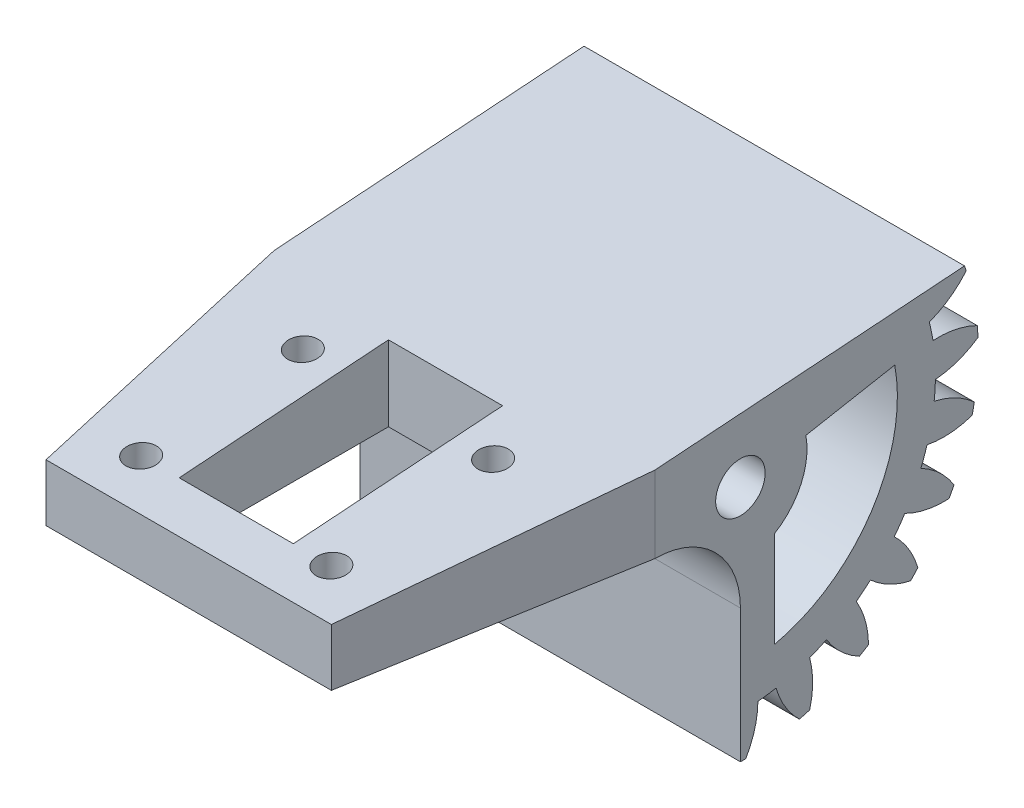
SolidWorks part; units mm, degrees
ref_plane "Plane1" through (0, 0, 0) normal (0, 0, 1) x (1, 0, 0)
ref_plane "Plane2" through (0, 0, 0) normal (0, 1, 0) x (1, 0, 0)
ref_plane "Plane3" through (0, 0, 0) normal (1, 0, 0) x (0, 0, -1)
other "Configuration Table"
sketch "HoldingSke" plane through (0, 0, 0) normal (0, 1, 0) x (1, 0, 0)
  line L0 (0, 0) -> (0.4603, -0.1954)
  line L1 (-15, 0) -> (100, 0) construction
  line L2 (0, 0) -> (-2.1039, 2.3779)
  line L3 (0, 0) -> (-11.863, 4.5341)
  line L4 (0, 0) -> (7.9495, 3.3744)
  line L5 (0, 0) -> (-46.8476, -17.4728)
  line L6 (0, 0) -> (-33.1585, -22.3721)
  line L7 (-2.1039, 2.3779) -> (8.6586, 51.2059)
  line L8 (-76.2, 54.61) -> (-76.1, 54.61)
  line L9 (-71.009, 38.7566) -> (-53.1078, 45.2721)
  line L10 (-76.2, 71.12) -> (104.1128, 71.12)
  line L11 (0, 0) -> (-40, 0)
  line L12 (-76.2, 101.6) -> (-76.133, 101.6)
  line L13 (24.9733, 27.94) -> (52.9518, 28.4284)
  line L14 (24.9733, 27.94) -> (24.9743, 27.94)
  line L15 (24.9733, 27.94) -> (100.4006, 29.5858)
  line L16 (-63.627, -2) -> (-12.827, -2)
  circle A0 centre (0, 0) radius 0.4
  circle A1 centre (0, 0) radius 20.499
  circle A2 centre (0, 0) radius 37.5
  circle A3 centre (0, 0) radius 0.4
  dimension "MHD" = 40.998
  dimension "Hub_dia" = 75
  dimension "Bore" = 0.8
  dimension "MBD" = 0.8
  dimension "Num_teeth" = 23
  dimension "Pitch" = 0.5
  dimension "Overall_len" = 50
  dimension "Show_teeth" = 23
  dimension "Thickness" = 40
  dimension "OAL" = 50.0001
  dimension "T_dim" = 0.1
  dimension "Ap" = 20
  dimension "H" = 19.05
  dimension "Pitch_radius" = 180.3128
  dimension "Width" = 40
  dimension "Backlash" = 0.067
  dimension "Addendum_fac" = 1
  dimension "Dedendum_fac" = 1.25
  dimension "Clearance_fac" = 0.25
  dimension "Dedendum_add" = 0.001
  dimension "Module" = 2
sketch "BasProSke" plane through (0, 0, 0) normal (0, 1, 0) x (1, 0, 0)
  line L0 (-10, 0) -> (60, 0) construction
  line L1 (0, 0) -> (0, 25)
  line L2 (0, 0) -> (40, 0)
  line L3 (40, 0) -> (40, 25)
  line L4 (40, 25) -> (0, 25)
  dimension "Thickness" = 40
  dimension "Diameter" = 50
revolve "Base-Revolve" add sketch "BasProSke" angle 360 about L0
sketch "TooCutSke" plane through (0, 0, 0) normal (1, 0, 0) x (0, 0, -1)
  line L1 (0, 0) -> (0, 107) construction
  line L2 (0, 0) -> (-1.6868, 22.9381) construction
  line L3 (0, 0) -> (-6.2512, 45.4806) construction
  line L4 (-1.6868, 22.9381) -> (-3.1256, 22.7403) construction
  arc A0 (0.9602, 20.4765) -> (-0.9602, 20.4765) centre (0, 0) ccw
  arc A1 (2.8652, 24.8608) -> (-2.8652, 24.8608) centre (0, 0) ccw
  circle A2 centre (0, 0) radius 23 construction
  circle A3 centre (0, 0) radius 21.6129 construction
  arc A4 (-0.9602, 20.4765) -> (-2.8652, 24.8608) centre (-10.0609, 19.1284) ccw
  arc A5 (2.8652, 24.8608) -> (0.9602, 20.4765) centre (10.0609, 19.1284) ccw
  dimension "Root_dia" = 40.998
  dimension "Overcut_dia" = 50.0508
  dimension "Pitch_dia" = 46
  dimension "Base_dia" = 43.2259
  dimension "Flank_rad" = 9.2
  dimension "Half_ang" = 7.826
  dimension "Half_CT" = 1.4523
extrude "ToothCut" cut sketch "TooCutSke" along normal through all
fillet "Breaks" [suppressed] radius 0.04
fillet "RootFillets" [suppressed] radius 0.501
pattern_circular "TeethCuts" count 23 every 15.652 about axis through (-10, 0, 0) along (1, 0, 0) of "ToothCut", "RootFillets", "Breaks"
sketch "HubNeaOneSke" plane through (0, 0, 0) normal (-1, 0, 0) x (0, 0, 1)
  circle A0 centre (0, 0) radius 20.499
  dimension "Diameter" = 40.998
extrude "HubNearOne" [suppressed] add sketch "HubNeaOneSke" along normal blind 10.0001
sketch "HubNeaBotSke" plane through (0, 0, 0) normal (-1, 0, 0) x (0, 0, 1)
  circle A0 centre (0, 0) radius 20.499
  dimension "Diameter" = 40.998
extrude "HubNearBoth" [suppressed] add sketch "HubNeaBotSke" along normal blind 5
ref_plane "FarPln" through (40, 0, 0) normal (1, 0, 0) x (0, 0, -1)
sketch "HubFarSke" plane through (40, 0, 0) normal (1, 0, 0) x (0, 0, -1)
  circle A0 centre (0, 0) radius 20.499
  dimension "Diameter" = 40.998
extrude "HubFar" [suppressed] add sketch "HubFarSke" along normal blind 5
sketch "BorSke" plane through (0, 0, 0) normal (1, 0, 0) x (0, 0, -1)
  circle A0 centre (0, 0) radius 0.4
  dimension "Diameter" = 0.8
extrude "Bore" cut sketch "BorSke" along normal mid plane 100.0001
sketch "KeySke" plane through (0, 0, 0) normal (1, 0, 0) x (0, 0, -1)
  line L0 (-0.05, 0) -> (-0.05, 0.5)
  line L1 (-0.05, 0.5) -> (0.05, 0.5)
  line L2 (0.05, 0.5) -> (0.05, 0)
  line L3 (0, 0) -> (0, 34) construction
  line L4 (-0.05, 0) -> (0.05, 0)
  dimension "Offset" = 0.5
  dimension "Width" = 0.1
extrude "Keyway" [suppressed] cut sketch "KeySke" along normal mid plane 100.0001
pattern_circular "Keyway2" [suppressed] count 2 every 90 about axis through (-10, 0, 0) along (1, 0, 0)
sketch "草图1" plane through (40, 0, 0) normal (1, 0, 0) x (0, 0, -1)
  line L0 (0, 0) -> (0, -25)
  line L3 (33.1445, 17.3715) -> (-10.0788, 32.7237)
  line L4 (-10.0788, 32.7237) -> (-39.8602, 4.3079)
  line L5 (-39.8602, 4.3079) -> (-13.135, -31.3257)
  line L6 (-13.135, -31.3257) -> (0, -25)
  line L7 (0, 0) -> (23.5565, 8.372)
  line L8 (23.5565, 8.372) -> (33.1445, 17.3715)
  arc A0 (-0.562, -24.9937) -> (0.562, -24.9937) centre (0, 0) ccw construction
  arc A2 (23.7388, 7.8403) -> (23.3624, 8.8994) centre (0, 0) ccw construction
extrude "切除-拉伸1" cut sketch "草图1" against normal through all
sketch "草图2" plane through (0, 0, 0) normal (-1, 0, 0) x (0, 0, 1)
  circle A0 centre (0, 0) radius 1.6
  dimension "D1" = 3.2
extrude "切除-拉伸2" cut sketch "草图2" against normal through all
sketch "草图4" plane through (40, 0, 0) normal (1, 0, 0) x (0, 0, -1)
  line L2 (0, -25) -> (0, -1.6) construction
  line L7 (0, -4) -> (0, -11)
  line L8 (0, -1.6) -> (0, -4)
  line L9 (-37.9995, -2) -> (-37.9995, 4)
  line L12 (1.5076, 0.5358) -> (23.5565, 8.372)
  line L13 (-37.9995, 4) -> (23.5565, 8.372)
  line L14 (0, 0) -> (-37.9995, 0) construction
  line L16 (-37.9995, -2) -> (-9, -2)
  arc A0 (1.5076, 0.5358) -> (0, -1.6) centre (0, 0) ccw
  arc A1 (0, -11) -> (-9, -2) centre (-9, -11) ccw
  dimension "D3" = 2
  dimension "D4" = 9
  dimension "D1" = 9
  dimension "D2" = 6
extrude "凸台-拉伸1" add sketch "草图4" against normal blind 40
sketch "草图5" plane through (0, -1, 0) normal (0, -1, 0) x (1, 0, 0)
  line L0 (20, 37.9995) -> (20, 4.7155) construction
  circle A0 centre (30, 15.9995) radius 1.6
  circle A1 centre (30, 32.9995) radius 1.6
  circle A2 centre (10, 32.9995) radius 1.6
  circle A3 centre (10, 15.9995) radius 1.6
  dimension "D1" = 10
  dimension "D3" = 10
extrude "切除-拉伸3" cut sketch "草图5" against normal through all
sketch "草图6" plane through (0, 0, 0) normal (-1, 0, 0) x (0, 0, 1)
  line L2 (-6.8825, 1.2774) -> (-16.223, 3.0109)
  line L3 (-23.5565, 8.372) -> (0, 4) construction
  line L4 (-3.5816, -6.0143) -> (-3.5816, -16.1066)
  arc A0 (-16.223, 3.0109) -> (-3.5816, -16.1066) centre (0, 0) ccw
  arc A1 (-6.8825, 1.2774) -> (-3.5816, -6.0143) centre (0, 0) ccw
extrude "切除-拉伸4" cut sketch "草图6" against normal through all
sketch "草图7" plane through (0, -1, 0) normal (0, -1, 0) x (1, 0, 0)
  line L0 (40, 22.9995) -> (0, 22.9995) construction
  line L3 (20, 37.9995) -> (20, 2.8797) construction
  line L5 (14, 32.9995) -> (26, 32.9995)
  line L7 (14, 10.9995) -> (14, 32.9995)
  line L9 (26, 10.9995) -> (26, 32.9995)
  line L10 (14, 10.9995) -> (26, 32.9995) construction
  line L11 (14, 32.9995) -> (26, 10.9995) construction
  line L12 (0, 37.9995) -> (40, 37.9995) construction
  line L13 (14, 10.9995) -> (26, 10.9995)
  point P10 (20, 21.9995)
  dimension "D1" = 6
  dimension "D2" = 22
  dimension "D3" = 5
extrude "切除-拉伸5" cut sketch "草图7" against normal through all
sketch "草图8" plane through (40, 0, 0) normal (1, 0, 0) x (0, 0, -1)
  circle A0 centre (0, 0) radius 2.6
extrude "切除-拉伸6" cut sketch "草图8" against normal through all
sketch "草图10" plane through (0, -1, 0) normal (0, 1, 0) x (1, 0, 0)
  line L0 (14, -10.9995) -> (14, -32.9995)
  line L1 (14, -32.9995) -> (26, -32.9995)
  line L2 (26, -32.9995) -> (26, -10.9995) construction
  line L3 (26, -10.9995) -> (26, -32.9995) construction
  line L4 (26, -32.9995) -> (26, -10.9995)
  line L5 (26, -10.9995) -> (14, -10.9995)
  circle A0 centre (10, -15.9995) radius 1.6
  circle A1 centre (10, -32.9995) radius 1.6
  circle A2 centre (30, -15.9995) radius 1.6
  circle A3 centre (30, -32.9995) radius 1.6
extrude "切除-拉伸7" cut sketch "草图10" against normal through all
ref_plane "基准面1" through (0, -2, 37.9995) normal (0, 0, -1) x (-1, 0, 0)
sketch "草图12" plane through (0, -2, 0) normal (0, -1, 0) x (1, 0, 0)
  line L0 (5, 37.9995) -> (0, 9)
  line L1 (5, 10.9995) -> (5, 87.9995) construction
  line L2 (0, 37.9995) -> (40, 37.9995) construction
  line L6 (20, 37.9995) -> (20, 10.9995) construction
  line L7 (14, 10.9995) -> (26, 10.9995) construction
  line L10 (35, 37.9995) -> (40, 9)
  line L11 (0, 9) -> (0, 37.9995)
  line L12 (0, 37.9995) -> (5, 37.9995)
  line L13 (40, 37.9995) -> (35, 37.9995)
  line L14 (40, 37.9995) -> (40, 9)
extrude "切除-拉伸9" cut sketch "草图12" against normal through all
equation "' \"Module@HoldingSke\" = 6.35"
equation "' \"Num_teeth@HoldingSke\" = 12"
equation "' \"Ap@HoldingSke\" =  20"
equation "' \"Ap@HoldingSke\" = 20"
equation "' \"Width@HoldingSke\" = 0.5 * 25.4"
equation "' \"Hub_dia@HoldingSke\"= 1 * 25.4"
equation "' \"Hub_dia@HoldingSke\" = 1 * 25.4"
equation "' \"Overall_len@HoldingSke\" = 1.0 * 25.4"
equation "' \"Bore@HoldingSke\" = 0.75 * 25.4"
equation "' \"T_dim@HoldingSke\" = 0.1 * 25.4"
equation "' \"Width@KeySke\" = 0.25 * 25.4"
equation "' \"Show_teeth@HoldingSke\" = 13"
equation "' \"Backlash@HoldingSke\" = 0.009 * 25.4"
equation "' \"Addendum_fac@HoldingSke\" = 1.0"
equation "' \"Dedendum_fac@HoldingSke\" = 1.25"
equation "' \"Dedendum_add@HoldingSke\" = 0.00005 * 25.4"
equation "' \"Clearance_fac@HoldingSke\" = 0.25"
equation "\"Pitch@HoldingSke\" = 1 / \"Module@HoldingSke\""
equation "\"Overcut_dia@TooCutSke\" = (\"Num_teeth@HoldingSke\" + 2 * \"Addendum_fac@HoldingSke\") / \"Pitch@HoldingSke\" + 0.002 * 25.4"
equation "\"Pitch_dia@TooCutSke\" = \"Num_teeth@HoldingSke\" / \"Pitch@HoldingSke\""
equation "\"Base_dia@TooCutSke\" = \"Num_teeth@HoldingSke\" / \"Pitch@HoldingSke\" * cos((\"Ap@HoldingSke\"  * 3.14159265 / 180))"
equation "\"Root_dia@TooCutSke\" = (\"Num_teeth@HoldingSke\" + 2) / \"Pitch@HoldingSke\" - 2 * (\"Addendum_fac@HoldingSke\" + \"Dedendum_fac@HoldingSke\") / \"Pitch@HoldingSke\" - \"Dedendum_add@HoldingSke\" * 2"
equation "\"Half_ang@TooCutSke\" = 180 / \"Num_teeth@HoldingSke\""
equation "\"Half_CT@TooCutSke\" = \"Num_teeth@HoldingSke\" / \"Pitch@HoldingSke\" * sin((3.14159265 / 2 / \"Num_teeth@HoldingSke\")) / 2 - 7 * \"Backlash@HoldingSke\" / 4"
equation "\"Flank_rad@TooCutSke\" = \"Num_teeth@HoldingSke\" / \"Pitch@HoldingSke\" / 5"
equation "\"Radius@RootFillets\" = \"Clearance_fac@HoldingSke\" / \"Pitch@HoldingSke\" + \"Dedendum_add@HoldingSke\""
equation "\"Break_rad@Breaks\" = 0.02 / \"Pitch@HoldingSke\""
equation "\"Thickness@HoldingSke\" = \"Width@HoldingSke\""
equation "\"OAL@HoldingSke\" = \"Thickness@HoldingSke\""
equation "\"MHD@HoldingSke\" = (\"Num_teeth@HoldingSke\" + 2) / \"Pitch@HoldingSke\" - 2 * (\"Addendum_fac@HoldingSke\" + \"Dedendum_fac@HoldingSke\")  / \"Pitch@HoldingSke\" - \"Dedendum_add@HoldingSke\" * 2"
equation "\"MBD@HoldingSke\" = (\"Num_teeth@HoldingSke\" + 2) / \"Pitch@HoldingSke\" - 2 * (\"Addendum_fac@HoldingSke\" + \"Dedendum_fac@HoldingSke\")  / \"Pitch@HoldingSke\" - \"Dedendum_add@HoldingSke\" * 2 - 0.002 * 25.4"
equation "\"MHD@HoldingSke\" = ((sgn( \"MHD@HoldingSke\" - \"Hub_dia@HoldingSke\" )-1)*( \"MHD@HoldingSke\" - \"Hub_dia@HoldingSke\" ))/-2+ \"Hub_dia@HoldingSke\""
equation "\"MBD@HoldingSke\" = ((sgn( \"MBD@HoldingSke\" - \"Bore@HoldingSke\" )-1)*( \"MBD@HoldingSke\" - \"Bore@HoldingSke\" ))/-2+ \"Bore@HoldingSke\""
equation "\"OAL@HoldingSke\" = ((sgn( \"OAL@HoldingSke\" - \"Overall_len@HoldingSke\" )+1)*( \"OAL@HoldingSke\" - \"Overall_len@HoldingSke\" ))/2 + \"Overall_len@HoldingSke\" + 0.000002 * 25.4"
equation "\"Num_teeth@TeethCuts\" = int( \"Show_teeth@HoldingSke\" ) + 1"
equation "\"Num_teeth@TeethCuts\" = ((sgn( \"Num_teeth@TeethCuts\" - \"Num_teeth@HoldingSke\" )-1)*( \"Num_teeth@TeethCuts\" - \"Num_teeth@HoldingSke\" ))/-2+ \"Num_teeth@HoldingSke\""
equation "\"Num_teeth@TeethCuts\" = ((sgn( \"Num_teeth@TeethCuts\" - 2.0)+1)*( \"Num_teeth@TeethCuts\" - 2.0))/2 +2.0"
equation "\"Angle@TeethCuts\" = 360.0 / \"Num_teeth@HoldingSke\""
equation "\"Diameter@BasProSke\" = (\"Num_teeth@HoldingSke\" + 2 * \"Addendum_fac@HoldingSke\") / \"Pitch@HoldingSke\""
equation "\"Thickness@BasProSke\"  = \"Thickness@HoldingSke\""
equation "' \"Fillet_rad@BasProSke\" =  \"Thickness@HoldingSke\" * 0.05"
equation "' \"Fillet_rad@BasProSke\" = \"Thickness@HoldingSke\" * 0.05"
equation "\"MHD@HoldingSke\" = ((sgn( \"MHD@HoldingSke\" - \"Root_dia@TooCutSke\" )-1)*( \"MHD@HoldingSke\" - \"Root_dia@TooCutSke\" ))/-2+ \"Root_dia@TooCutSke\""
equation "\"Diameter@HubNeaOneSke\" = \"MHD@HoldingSke\""
equation "\"Length@HubNearOne\" = \"OAL@HoldingSke\" - \"Thickness@BasProSke\""
equation "\"Diameter@HubNeaBotSke\" = \"MHD@HoldingSke\""
equation "\"Length@HubNearBoth\" = ( \"OAL@HoldingSke\" - \"Thickness@BasProSke\" ) / 2.0"
equation "\"Thickness@FarPln\" = \"Thickness@BasProSke\""
equation "\"Diameter@HubFarSke\" = \"MHD@HoldingSke\""
equation "\"Length@HubFar\" = ( \"OAL@HoldingSke\" - \"Thickness@BasProSke\" ) / 2.0"
equation "\"Diameter@BorSke\" = \"MBD@HoldingSke\""
equation "\"D1@Bore\" = \"OAL@HoldingSke\" * 2.0"
equation "\"D1@Keyway\" = \"OAL@HoldingSke\" * 2.0"
equation "\"Offset@KeySke\" = \"T_dim@HoldingSke\" + \"MBD@HoldingSke\" / 2.0"
